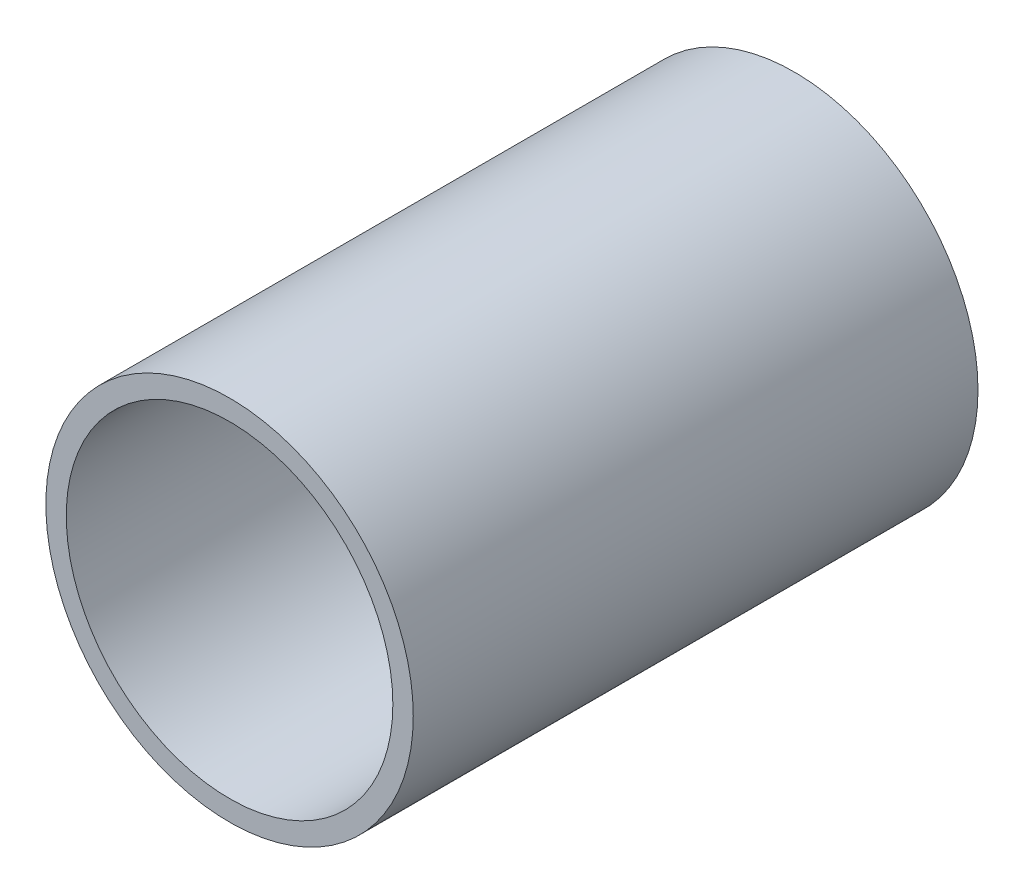
SolidWorks part; units mm, degrees
ref_plane "Płaszczyzna przednia" through (0, 0, 0) normal (0, 0, 1) x (1, 0, 0)
ref_plane "Płaszczyzna górna" through (0, 0, 0) normal (0, 1, 0) x (1, 0, 0)
ref_plane "Płaszczyzna prawa" through (0, 0, 0) normal (1, 0, 0) x (0, 0, -1)
sketch "Szkic1" plane through (0, 0, 0) normal (0, 0, 1) x (1, 0, 0)
  circle A0 centre (0, 0) radius 12
  circle A1 centre (0, 0) radius 13.5
  dimension "D1" = 24
  dimension "D2" = 27
extrude "Dodanie-wyciągnięcie1" add sketch "Szkic1" along normal blind 41.5
